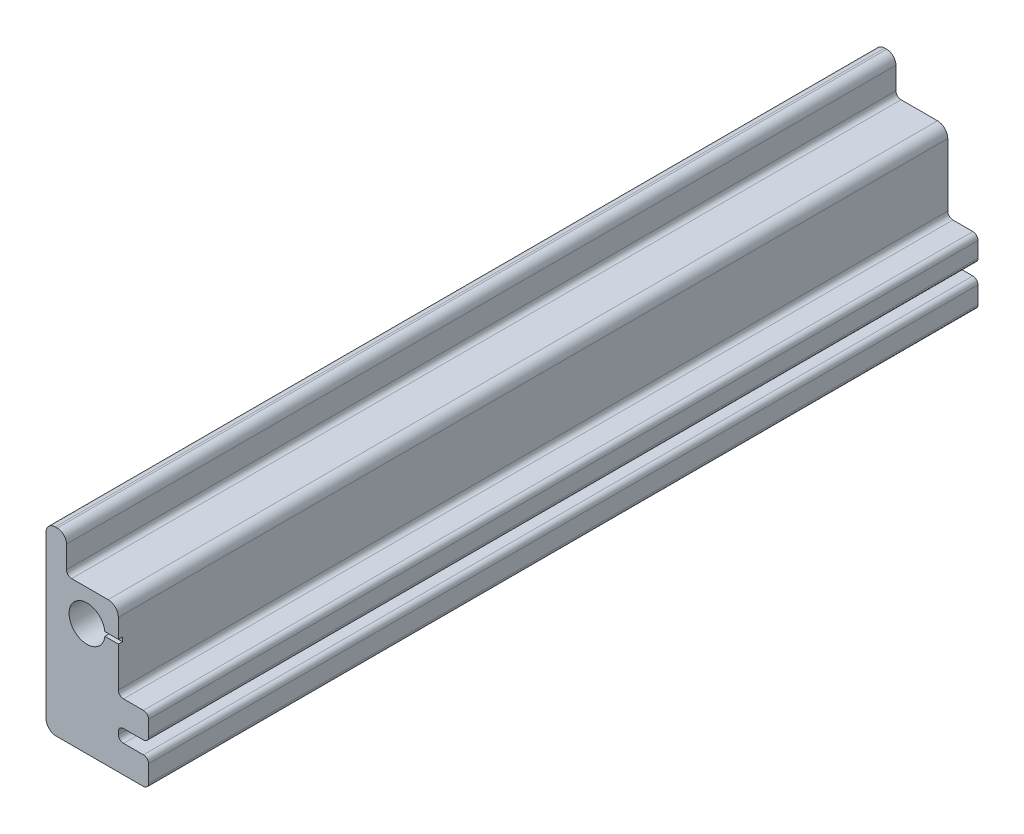
SolidWorks part; units mm, degrees
material "Pink Foam"
ref_plane "Front Plane" through (0, 0, 0) normal (0, 0, 1) x (1, 0, 0)
ref_plane "Top Plane" through (0, 0, 0) normal (0, 1, 0) x (1, 0, 0)
ref_plane "Right Plane" through (0, 0, 0) normal (1, 0, 0) x (0, 0, -1)
sketch "Sketch1" plane through (0, 0, 0) normal (0, 0, 1) x (1, 0, 0)
  line L1 (34.925, -69.85) -> (-19.05, -69.85)
  line L2 (38.1, -41.7472) -> (38.1, -32.2222)
  line L3 (34.925, -29.0472) -> (22.5628, -29.0472)
  line L4 (-25.4, -63.5) -> (-25.4, 36.2978)
  line L6 (19.3878, -25.8722) -> (19.3878, 13.0378)
  line L7 (13.0378, 19.3878) -> (-9.525, 19.3878)
  line L8 (-12.7, 22.5628) -> (-12.7, 36.2978)
  line L9 (-18.415, 42.0128) -> (-19.685, 42.0128)
  line L11 (34.925, -44.9222) -> (22.5628, -44.9222)
  line L12 (11.1125, 0) -> (19.3878, 0) construction
  line L14 (0, 11.1125) -> (0, 19.3878) construction
  line L15 (19.3878, -48.0972) -> (19.3878, -49.6847)
  line L19 (22.5628, -52.8597) -> (34.925, -52.8597)
  line L20 (38.1, -66.675) -> (38.1, -56.0347)
  circle A0 centre (0, 0) radius 11.1125
  arc A3 (-9.525, 19.3878) -> (-12.7, 22.5628) centre (-9.525, 22.5628) cw
  arc A4 (-19.05, -69.85) -> (-25.4, -63.5) centre (-19.05, -63.5) cw
  arc A6 (38.1, -32.2222) -> (34.925, -29.0472) centre (34.925, -32.2222) ccw
  arc A8 (19.3878, 13.0378) -> (13.0378, 19.3878) centre (13.0378, 13.0378) ccw
  arc A9 (-12.7, 36.2978) -> (-18.415, 42.0128) centre (-18.415, 36.2978) ccw
  arc A10 (-19.685, 42.0128) -> (-25.4, 36.2978) centre (-19.685, 36.2978) ccw
  arc A11 (19.3878, -25.8722) -> (22.5628, -29.0472) centre (22.5628, -25.8722) ccw
  arc A12 (22.5628, -44.9222) -> (19.3878, -48.0972) centre (22.5628, -48.0972) ccw
  arc A13 (34.925, -44.9222) -> (38.1, -41.7472) centre (34.925, -41.7472) ccw
  arc A14 (22.5628, -52.8597) -> (19.3878, -49.6847) centre (22.5628, -49.6847) cw
  arc A15 (34.925, -69.85) -> (38.1, -66.675) centre (34.925, -66.675) ccw
  arc A16 (34.925, -52.8597) -> (38.1, -56.0347) centre (34.925, -56.0347) cw
  point P9 (0, -11.1125)
  point P15 (0, 11.1125)
  point P16 (11.1125, 0)
  point P31 (-12.7, 19.3878)
  point P34 (-25.4, -69.85)
  point P40 (38.1, -29.0472)
  point P47 (-12.7, 42.0128)
  point P50 (-25.4, 42.0128)
  point P56 (19.3878, -52.8597)
  point P59 (38.1, -69.85)
  point P62 (38.1, -52.8597)
  dimension "D1" = 22.225
  dimension "D6" = 8.2753
  dimension "D10" = 3.175
  dimension "D11" = 6.35
  dimension "D12" = 5.715
  dimension "D5" = 3.175
  dimension "D7" = 6.35
  dimension "D13" = 29.0472
  dimension "D14" = 3.175
  dimension "D15" = 18.7122
  dimension "D16" = 3.175
  dimension "D17" = 3.175
  dimension "D18" = 15.875
  dimension "D20" = 3.175
  dimension "D21" = 3.175
  dimension "D22" = 3.175
  dimension "D3" = 69.85
  dimension "D4" = 25.4
  dimension "D8" = 22.625
  dimension "D9" = 12.7
  dimension "D19" = 19.3878
  dimension "D23" = 7.9375
extrude "Boss-Extrude1" add sketch "Sketch1" along normal blind 513.461
sketch "Sketch2" plane through (0, 0, 513.461) normal (0, 0, 1) x (1, 0, 0)
  line L0 (13.0378, 19.3878) -> (-9.525, 19.3878) construction
  line L1 (-1.27, 19.3878) -> (1.27, 19.3878) construction
  line L2 (-1.27, 19.3878) -> (-1.27, 0) construction
  line L3 (-1.27, 0) -> (1.27, 0) construction
  line L4 (1.27, 19.3878) -> (1.27, 0) construction
  line L5 (-1.27, 9.6939) -> (0, 9.6939) construction
  line L6 (0, 9.6939) -> (1.27, 9.6939) construction
  line L7 (0, 9.6939) -> (0, 0) construction
  line L8 (19.3878, -25.8722) -> (19.3878, 13.0378) construction
  line L9 (-1.27, 1.27) -> (19.3878, 1.27)
  line L10 (-1.27, 1.27) -> (-1.27, -1.27)
  line L11 (-1.27, -1.27) -> (19.3878, -1.27)
  line L12 (19.3878, 1.27) -> (19.3878, -1.27)
  line L13 (9.0589, -1.27) -> (9.0589, 1.27) construction
  line L14 (9.0589, 0) -> (-1.27, 0) construction
  dimension "D1" = 2.54
  dimension "D2" = 2.54
extrude "Cut-Extrude1" cut sketch "Sketch2" against normal blind 2.54
